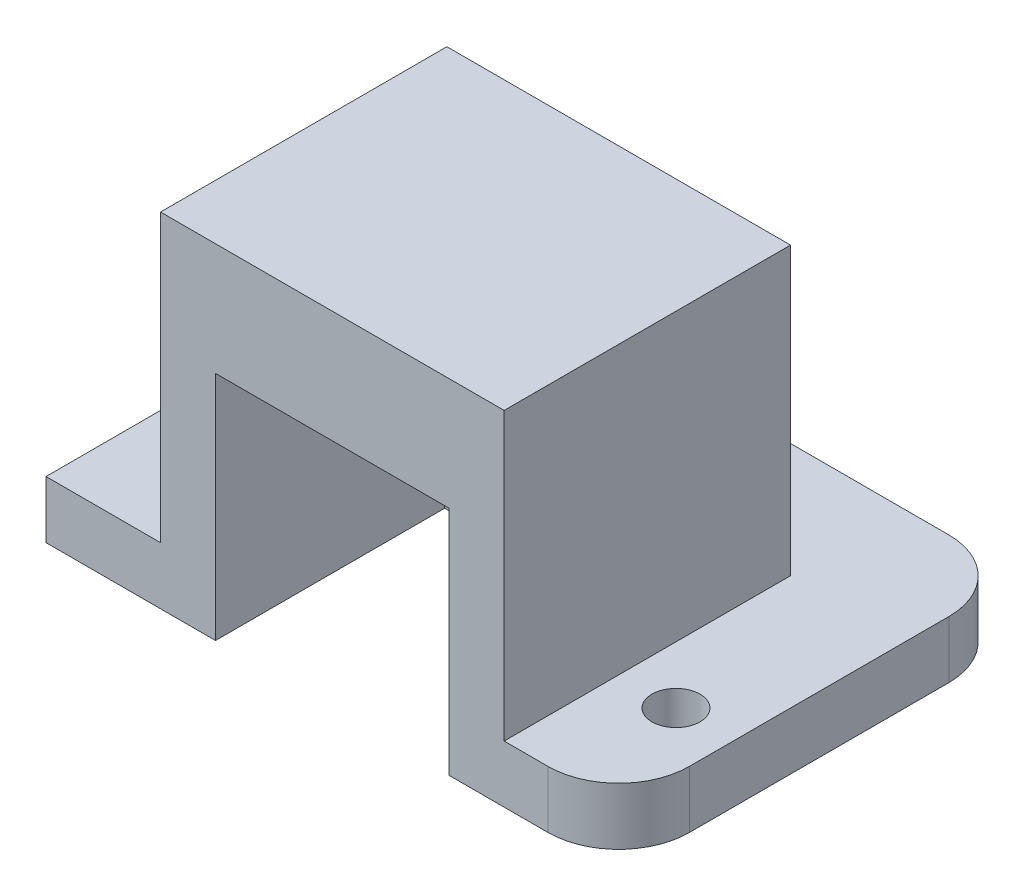
SolidWorks part; units mm, degrees
ref_plane "정면" through (0, 0, 0) normal (0, 0, 1) x (1, 0, 0)
ref_plane "윗면" through (0, 0, 0) normal (0, 1, 0) x (1, 0, 0)
ref_plane "우측면" through (0, 0, 0) normal (1, 0, 0) x (0, 0, -1)
sketch "스케치1" plane through (0, 0, 0) normal (0, 0, 1) x (1, 0, 0)
  line L1 (-15, 15) -> (15, 15)
  line L2 (-15, 15) -> (-15, -15)
  line L3 (-15, -15) -> (15, -15)
  line L4 (15, 15) -> (15, -15)
  line L5 (-15, 15) -> (15, -15) construction
  line L6 (-15, -15) -> (15, 15) construction
  point P4 (0, 0)
  point P5 (0, 0)
  point P6 (0, 0)
  dimension "D1" = 30
  dimension "D2" = 30
extrude "보스-돌출1" add sketch "스케치1" along normal blind 5 contours L1 L4 L3 L2
sketch "스케치2" plane through (0, 0, 0) normal (0, 0, -1) x (-1, 0, 0)
  line L0 (15, 15) -> (15, -15) construction
  line L1 (-15, -15) -> (15, -15)
  line L2 (-15, -15) -> (-15, -10)
  line L3 (-15, -10) -> (15, -10)
  line L4 (15, -15) -> (15, -10)
  line L5 (-15, -15) -> (15, -10) construction
  line L6 (-15, -10) -> (15, -15) construction
  point P4 (0, -12.5)
  dimension "D1" = 5
extrude "보스-돌출2" add sketch "스케치2" along normal blind 10
sketch "스케치3" plane through (0, -10, 0) normal (0, 1, 0) x (1, 0, 0)
  line L0 (-15, 10) -> (15, 10) construction
  circle A0 centre (0, 5) radius 2.1
  point P4 (0, 0)
  point P5 (0, 0)
  point P6 (0, 10)
  dimension "D1" = 4.2
  dimension "D2" = 5
extrude "컷-돌출1" cut sketch "스케치3" against normal blind 5
sketch "스케치4" plane through (0, 0, 5) normal (0, 0, 1) x (1, 0, 0)
  line L0 (10.2, -15) -> (15, -15)
  line L1 (-15, -15) -> (-10.2, -15)
  line L2 (-15, -15) -> (-15, 15)
  line L3 (-15, 15) -> (15, 15)
  line L4 (15, -15) -> (15, 15)
  line L5 (-15, -15) -> (15, 15) construction
  line L6 (-15, 15) -> (15, -15) construction
  line L8 (-10.2, -15) -> (-10.2, 5.2)
  line L9 (-10.2, 5.2) -> (10.2, 5.2)
  line L10 (10.2, -15) -> (10.2, 5.2)
  line L11 (-10.2, -15) -> (10.2, 5.2) construction
  line L12 (-10.2, 5.2) -> (10.2, -15) construction
  point P4 (0, 0)
  point P11 (0, -4.9)
  dimension "D1" = 4.8
  dimension "D2" = 4.8
  dimension "D3" = 9.8
extrude "보스-돌출3" add sketch "스케치4" along normal blind 20
sketch "스케치5" plane through (-15, 0, 0) normal (-1, 0, 0) x (0, 0, 1)
  line L0 (25, 15) -> (25, -15) construction
  line L1 (-10, -15) -> (25, -15)
  line L2 (-10, -15) -> (-10, -10)
  line L3 (-10, -10) -> (25, -10)
  line L4 (25, -15) -> (25, -10)
  line L5 (-10, -15) -> (25, -10) construction
  line L6 (-10, -10) -> (25, -15) construction
  point P4 (7.5, -12.5)
  dimension "D1" = 5
extrude "보스-돌출4" add sketch "스케치5" along normal blind 10
sketch "스케치6" plane through (15, 0, 0) normal (1, 0, 0) x (0, 0, -1)
  line L1 (-25, -15) -> (10, -15)
  line L2 (-25, -15) -> (-25, -10)
  line L3 (-25, -10) -> (10, -10)
  line L4 (10, -15) -> (10, -10)
  line L5 (-25, -15) -> (10, -10) construction
  line L6 (-25, -10) -> (10, -15) construction
  point P4 (-7.5, -12.5)
extrude "보스-돌출5" add sketch "스케치6" along normal blind 10
sketch "스케치7" plane through (0, -10, 0) normal (0, 1, 0) x (1, 0, 0)
  line L0 (-25, -25) -> (-25, 10) construction
  line L1 (25, 10) -> (25, -25) construction
  line L2 (-25, -25) -> (-15, -25) construction
  circle A0 centre (-20, -15) radius 2.1
  circle A1 centre (20, -15) radius 2.1
  point P8 (0, 0)
  dimension "D1" = 4.2
  dimension "D2" = 5
  dimension "D3" = 5
  dimension "D4" = 10
extrude "컷-돌출2" cut sketch "스케치7" against normal blind 10
fillet "필렛1" radius 6.17 1 edges at (25, -12.5, 25)
fillet "필렛2" radius 6.17 1 edges at (25, -12.5, -10)
